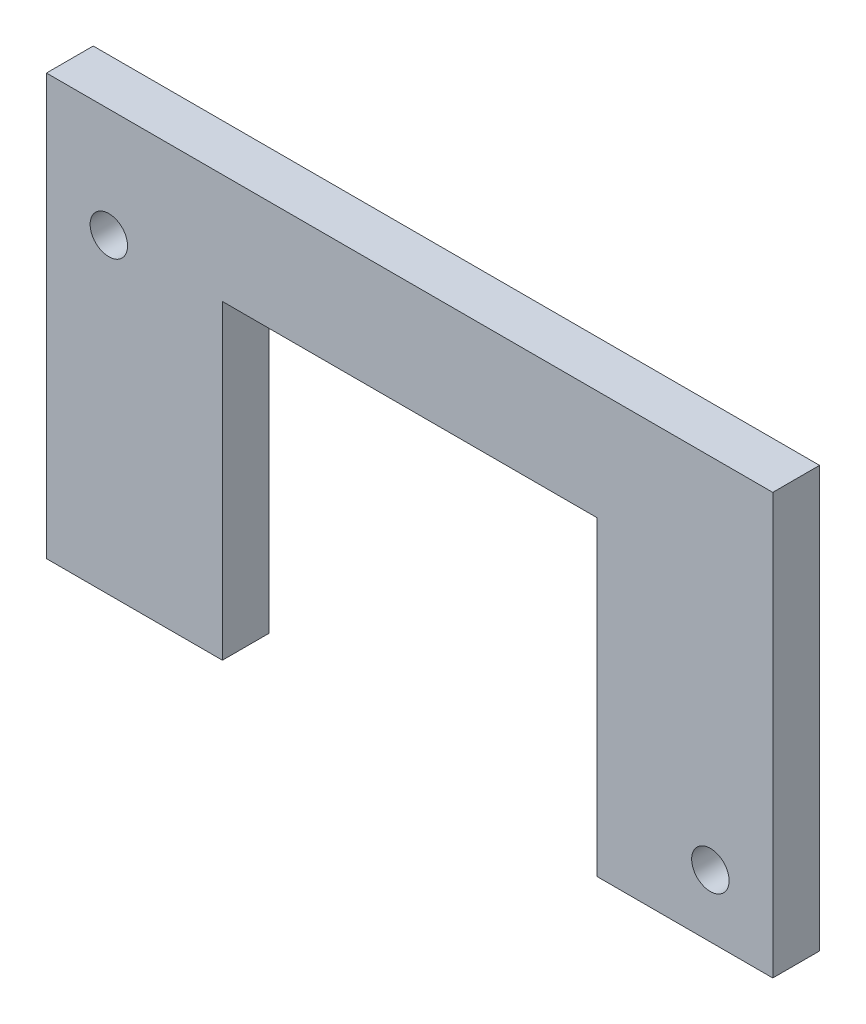
SolidWorks part; units mm, degrees
ref_plane "Front Plane" through (0, 0, 0) normal (0, 0, 1) x (1, 0, 0)
ref_plane "Top Plane" through (0, 0, 0) normal (0, 1, 0) x (1, 0, 0)
ref_plane "Right Plane" through (0, 0, 0) normal (1, 0, 0) x (0, 0, -1)
sketch "Sketch1" plane through (0, 0, 0) normal (0, 0, 1) x (1, 0, 0)
  line L1 (0, 0) -> (33.782, 0) construction
  line L2 (0, 0) -> (0, 19.812) construction
  line L3 (0, 19.812) -> (33.782, 19.812) construction
  line L4 (33.782, 0) -> (33.782, 19.812) construction
  line L5 (-1.5875, -1.5875) -> (35.3695, -1.5875)
  line L6 (-1.5875, -1.5875) -> (-1.5875, 19.812)
  line L7 (-1.5875, 19.812) -> (35.3695, 19.812)
  line L8 (35.3695, -1.5875) -> (35.3695, 19.812)
  circle A0 centre (1.5875, 14.2558) radius 0.9525
  circle A1 centre (32.1945, 1.5875) radius 0.9525
  dimension "D3" = 1.905
  dimension "0.065" = 1.905
  dimension "D5" = 1.5875
  dimension "D6" = 1.5875
  dimension "D7" = 1.5875
  dimension "D8" = 5.5562
  dimension "D9" = 3.175
  dimension "D11" = 3.175
  dimension "D12" = 5.5562
  dimension "D1" = 19.812
  dimension "D2" = 33.782
  dimension "D10" = 3.175
extrude "Boss-Extrude1" add sketch "Sketch1" along normal blind 2.3813
sketch "Sketch2" plane through (0, 0, 2.3813) normal (0, 0, 1) x (1, 0, 0)
  line L5 (-1.5875, -1.5875) -> (35.3695, -1.5875) construction
  line L6 (7.366, -1.5875) -> (26.416, -1.5875)
  line L7 (7.366, -1.5875) -> (7.366, 14.224)
  line L8 (7.366, 14.224) -> (26.416, 14.224)
  line L9 (26.416, -1.5875) -> (26.416, 14.224)
  line L10 (-1.5875, -1.5875) -> (7.366, -1.5875) construction
  line L11 (26.416, -1.5875) -> (35.3695, -1.5875) construction
  line L12 (35.3695, 19.812) -> (-1.5875, 19.812) construction
  dimension "D1" = 19.05
  dimension "D2" = 5.588
extrude "Cut-Extrude1" cut sketch "Sketch2" against normal up to next
